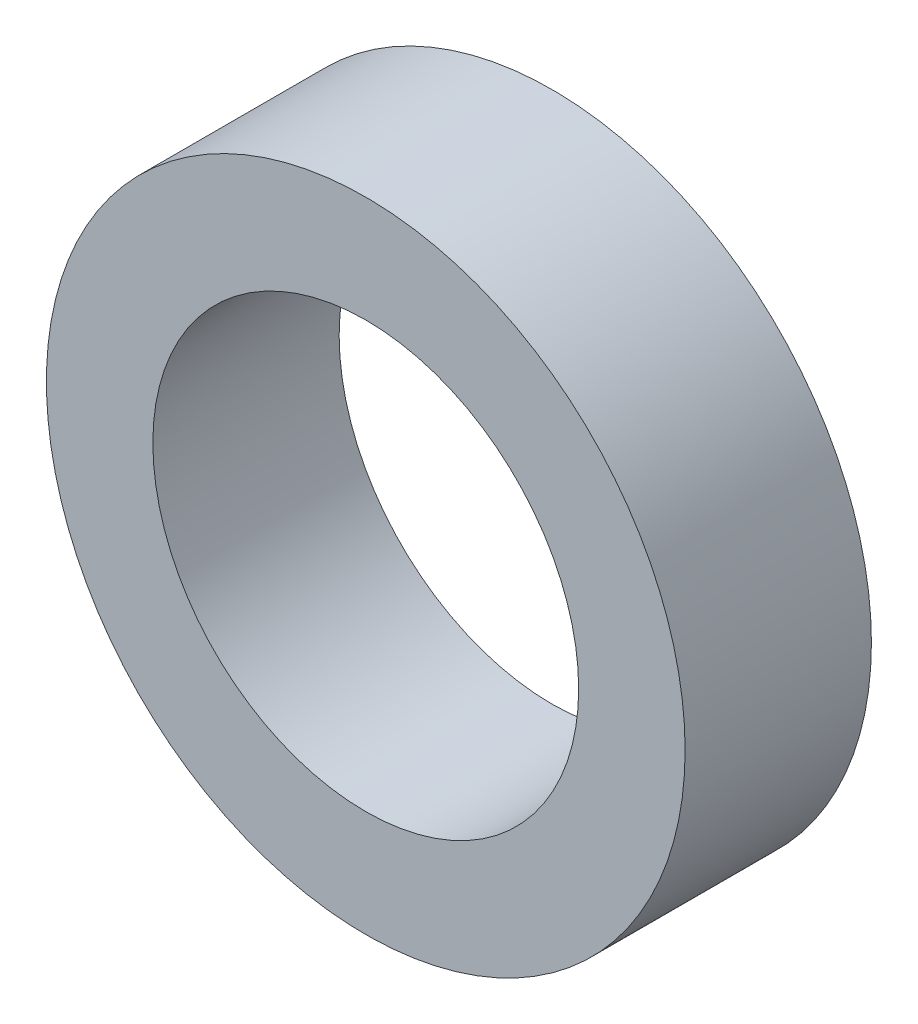
SolidWorks part; units mm, degrees
ref_plane "Plan de face" through (0, 0, 0) normal (0, 0, 1) x (1, 0, 0)
ref_plane "Plan de dessus" through (0, 0, 0) normal (0, 1, 0) x (1, 0, 0)
ref_plane "Plan de droite" through (0, 0, 0) normal (1, 0, 0) x (0, 0, -1)
sketch "Esquisse1" plane through (0, 0, 0) normal (0, 0, 1) x (1, 0, 0)
  circle A0 centre (0, 0) radius 4
  circle A1 centre (0, 0) radius 6
extrude "Extrusion1" add sketch "Esquisse1" along normal blind 3.5
